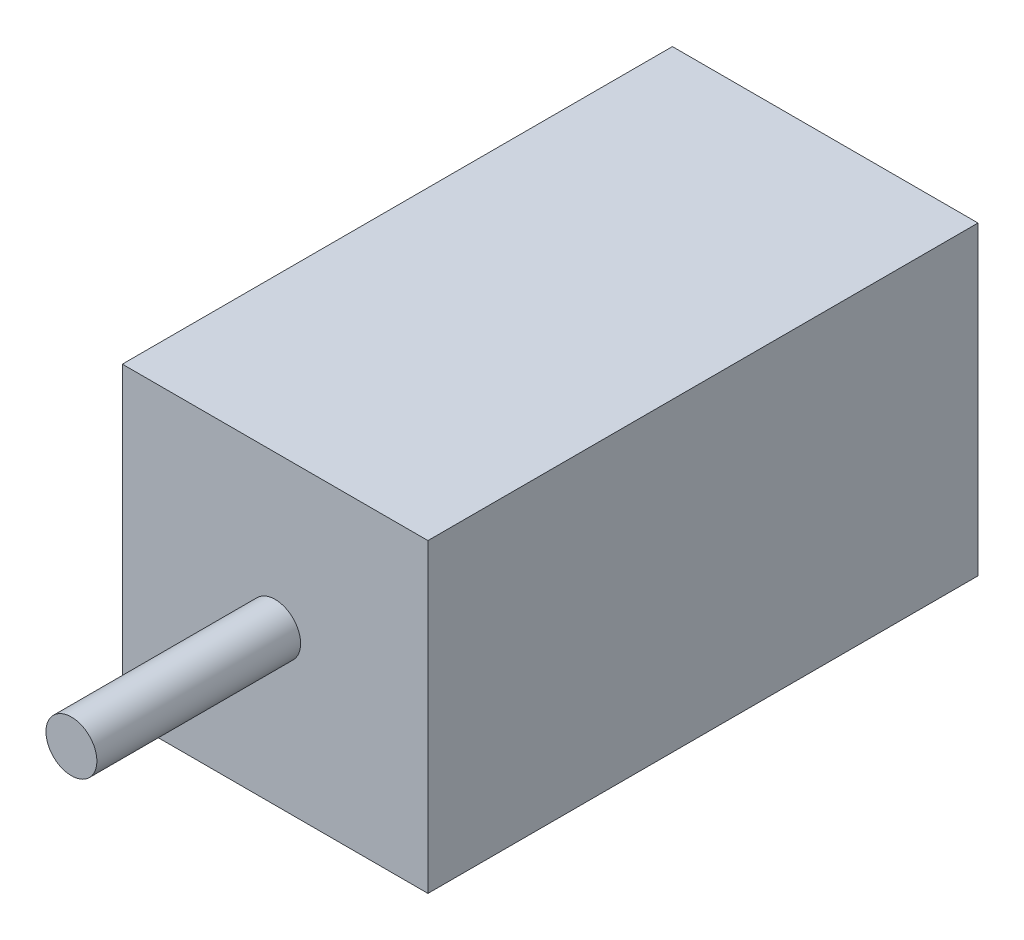
SolidWorks part; units mm, degrees
ref_plane "Front Plane" through (0, 0, 0) normal (0, 0, 1) x (1, 0, 0)
ref_plane "Top Plane" through (0, 0, 0) normal (0, 1, 0) x (1, 0, 0)
ref_plane "Right Plane" through (0, 0, 0) normal (1, 0, 0) x (0, 0, -1)
sketch "Sketch1" plane through (0, 0, 0) normal (0, 0, 1) x (1, 0, 0)
  line L1 (0, 0) -> (15, 0)
  line L2 (0, 0) -> (0, -15)
  line L3 (0, -15) -> (15, -15)
  line L4 (15, 0) -> (15, -15)
  dimension "D1" = 15
  dimension "D2" = 15
extrude "Boss-Extrude1" add sketch "Sketch1" along normal blind 27
sketch "Sketch2" plane through (0, 0, 27) normal (0, 0, 1) x (1, 0, 0)
  line L0 (15, 0) -> (0, 0) construction
  line L1 (0, 0) -> (0, -15) construction
  circle A0 centre (7.5, -7.5) radius 1.25
  point P2 (7.5, 0)
  point P3 (0, -7.5)
  point P6 (0, 0)
  point P9 (0, 0)
  dimension "D1" = 2.5
extrude "Boss-Extrude2" add sketch "Sketch2" along normal blind 10
